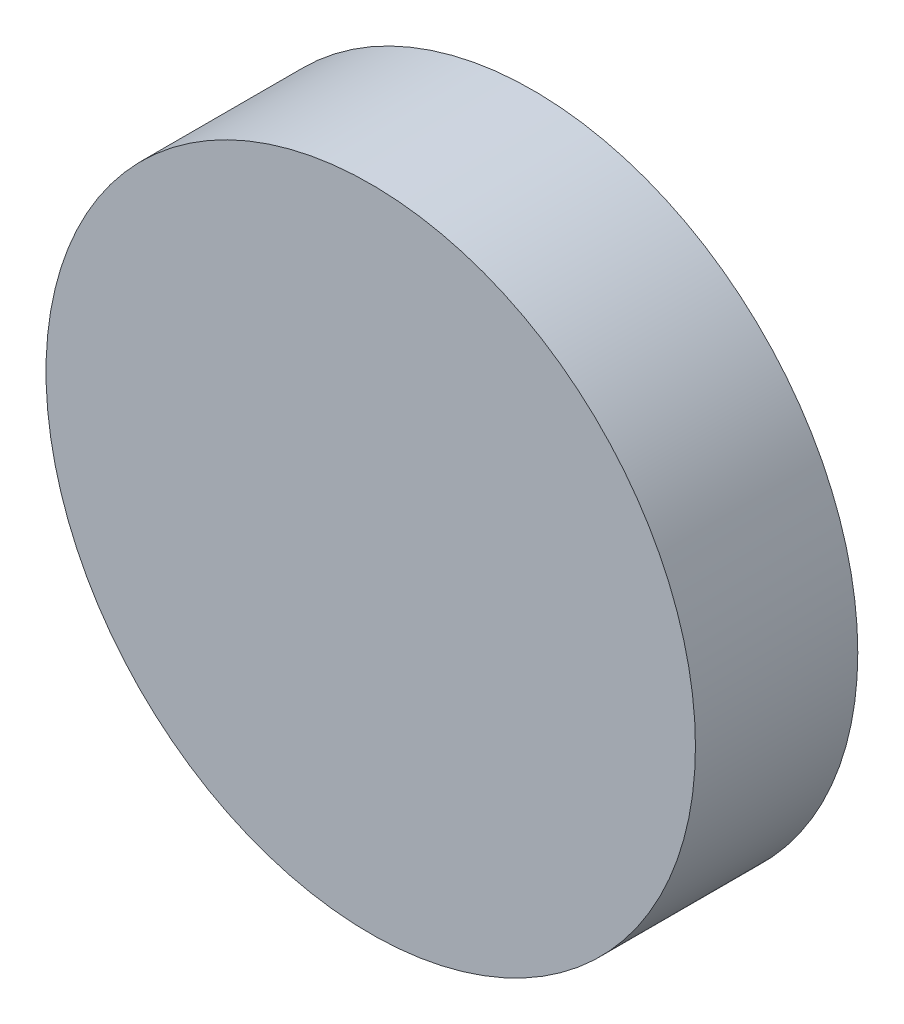
SolidWorks part; units mm, degrees
ref_plane "Front Plane" through (0, 0, 0) normal (0, 0, 1) x (1, 0, 0)
ref_plane "Top Plane" through (0, 0, 0) normal (0, 1, 0) x (1, 0, 0)
ref_plane "Right Plane" through (0, 0, 0) normal (1, 0, 0) x (0, 0, -1)
sketch "Sketch1" plane through (0, 0, 0) normal (0, 0, 1) x (1, 0, 0)
  circle A0 centre (0, 0) radius 10
  dimension "D1" = 20
extrude "Boss-Extrude1" add sketch "Sketch1" along normal blind 5 contours A0
